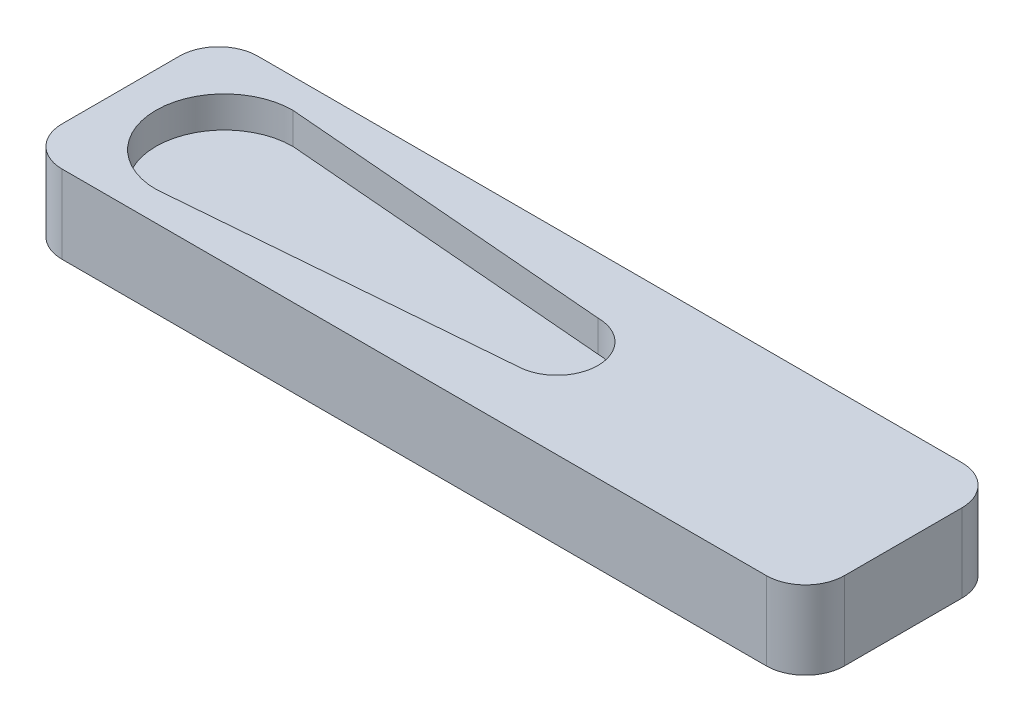
SolidWorks part; units mm, degrees
ref_plane "정면" through (0, 0, 0) normal (0, 0, 1) x (1, 0, 0)
ref_plane "윗면" through (0, 0, 0) normal (0, 1, 0) x (1, 0, 0)
ref_plane "우측면" through (0, 0, 0) normal (1, 0, 0) x (0, 0, -1)
sketch "스케치1" plane through (0, 0, 0) normal (0, 1, 0) x (1, 0, 0)
  line L1 (-20, -5) -> (20, -5)
  line L2 (-20, -5) -> (-20, 5)
  line L3 (-20, 5) -> (20, 5)
  line L4 (20, -5) -> (20, 5)
  line L5 (-20, -5) -> (20, 5) construction
  line L6 (-20, 5) -> (20, -5) construction
  point P0 (0, 0)
  dimension "D1" = 40
  dimension "D2" = 10
extrude "보스-돌출1" add sketch "스케치1" along normal blind 4
sketch "스케치2" plane through (0, 4, 0) normal (0, 1, 0) x (1, 0, 0)
  line L1 (-14.7033, -3.5) -> (2.2967, -2.1)
  line L2 (-55, 0) -> (55, 0) construction
  line L3 (0.1967, 0) -> (2.2967, 0) construction
  line L4 (-14.7033, 3.5) -> (2.2967, 2.1)
  arc A2 (2.2967, -2.1) -> (2.2967, 2.1) centre (2.2967, 0) ccw
  arc A3 (-14.7033, 3.5) -> (-14.7033, -3.5) centre (-14.7033, 0) ccw
  point P3 (-14.7033, 0)
  dimension "D1" = 7
extrude "컷-돌출1" cut sketch "스케치2" against normal blind 1.6
fillet "필렛1" radius 2 4 edges at (20, 2, 5) (20, 2, -5) (-20, 2, 5) (-20, 2, -5)
